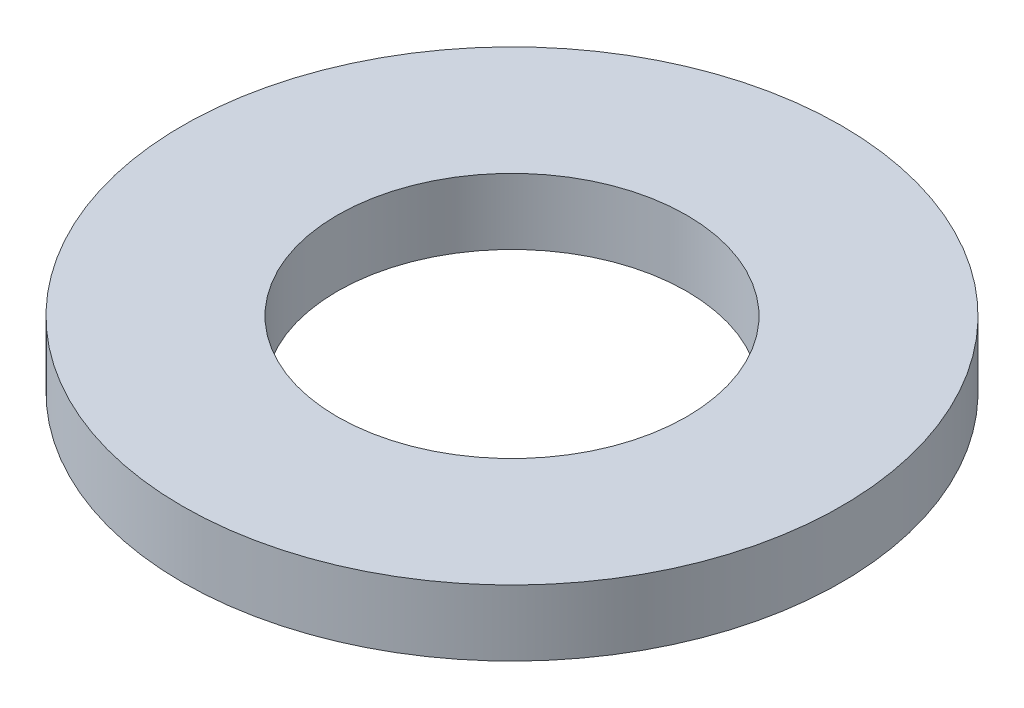
SolidWorks part; units mm, degrees
material "Chrome Stainless Steel"
ref_plane "Front Plane" through (0, 0, 0) normal (0, 0, 1) x (1, 0, 0)
ref_plane "Top Plane" through (0, 0, 0) normal (0, 1, 0) x (1, 0, 0)
ref_plane "Right Plane" through (0, 0, 0) normal (1, 0, 0) x (0, 0, -1)
sketch "Sketch1" plane through (0, 0, 0) normal (0, 1, 0) x (1, 0, 0)
  circle A0 centre (0, 0) radius 2.65
  circle A1 centre (0, 0) radius 5
  dimension "D1" = 5.3
  dimension "D2" = 10
extrude "Extrude1" add sketch "Sketch1" along normal blind 1
